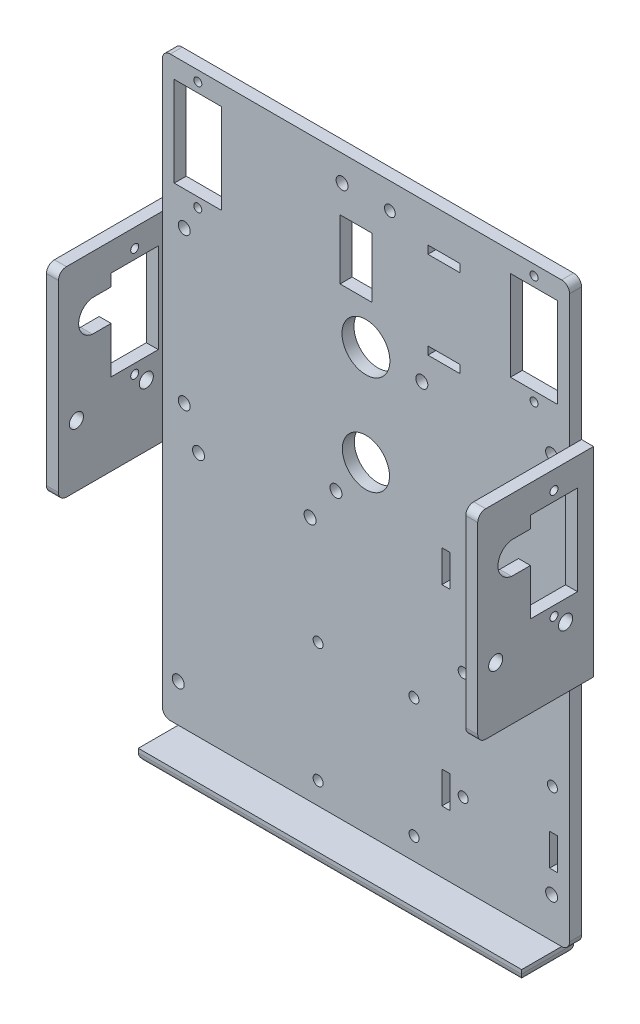
SolidWorks part; units mm, degrees
ref_plane "Alzado" through (0, 0, 0) normal (0, 0, 1) x (1, 0, 0)
ref_plane "Planta" through (0, 0, 0) normal (0, 1, 0) x (1, 0, 0)
ref_plane "Vista lateral" through (0, 0, 0) normal (1, 0, 0) x (0, 0, -1)
sketch "Model" plane through (0, 0, 0) normal (0, 0, 1) x (1, 0, 0)
  line L0 (13.199, -198.586) -> (108.1426, -198.586)
  line L1 (60.6708, -93.0989) -> (60.6708, -118.0989) construction
  line L2 (111.6708, -139.1347) -> (111.6708, -196.586)
  line L3 (111.6708, -139.1347) -> (114.6708, -139.1347)
  line L4 (114.6708, -89.1347) -> (114.6708, -139.1347)
  line L5 (111.6708, -89.1347) -> (114.6708, -89.1347)
  line L6 (111.6708, -56.021) -> (111.6708, -89.1347)
  line L7 (6.6708, -89.1347) -> (6.6708, -139.1347)
  line L8 (11.6708, -198.586) -> (13.199, -198.586)
  line L9 (109.6708, -198.586) -> (108.1426, -198.586)
  line L10 (77.899, -54.021) -> (43.5553, -54.021)
  line L13 (109.6708, -54.021) -> (77.899, -54.021)
  line L32 (9.6708, -139.1347) -> (9.6708, -196.586)
  line L35 (9.6708, -139.1347) -> (6.6708, -139.1347)
  line L37 (9.6708, -89.1347) -> (6.6708, -89.1347)
  line L40 (9.6708, -56.021) -> (9.6708, -89.1347)
  line L41 (43.5553, -54.021) -> (11.6708, -54.021)
  line L48 (54.199, -67.627) -> (54.199, -82.627)
  line L49 (54.199, -82.627) -> (62.199, -82.627)
  line L50 (62.199, -82.627) -> (62.199, -67.627)
  line L51 (62.199, -67.627) -> (54.199, -67.627)
  line L52 (76.199, -65.1868) -> (84.199, -65.1868)
  line L53 (84.199, -65.1868) -> (84.199, -63.1868)
  line L54 (84.199, -63.1868) -> (76.199, -63.1868)
  line L55 (76.199, -63.1868) -> (76.199, -65.1868)
  line L56 (76.199, -87.0675) -> (84.199, -87.0675)
  line L57 (84.199, -87.0675) -> (84.199, -85.0675)
  line L58 (84.199, -85.0675) -> (76.199, -85.0675)
  line L59 (76.199, -85.0675) -> (76.199, -87.0675)
  line L60 (96.8708, -59.021) -> (96.8708, -81.521)
  line L61 (96.8708, -81.521) -> (108.6708, -81.521)
  line L62 (108.6708, -81.521) -> (108.6708, -59.021)
  line L63 (108.6708, -59.021) -> (96.8708, -59.021)
  line L64 (24.4708, -59.021) -> (12.6708, -59.021)
  line L65 (12.6708, -59.021) -> (12.6708, -81.521)
  line L66 (12.6708, -81.521) -> (24.4708, -81.521)
  line L67 (24.4708, -81.521) -> (24.4708, -59.021)
  line L68 (81.699, -183.086) -> (81.699, -175.086)
  line L69 (81.699, -175.086) -> (79.699, -175.086)
  line L70 (79.699, -175.086) -> (79.699, -183.086)
  line L71 (79.699, -183.086) -> (81.699, -183.086)
  line L72 (108.6708, -183.086) -> (108.6708, -175.086)
  line L73 (108.6708, -175.086) -> (106.6708, -175.086)
  line L74 (106.6708, -175.086) -> (106.6708, -183.086)
  line L75 (106.6708, -183.086) -> (108.6708, -183.086)
  line L76 (81.699, -135.086) -> (81.699, -127.086)
  line L77 (81.699, -127.086) -> (79.699, -127.086)
  line L78 (79.699, -127.086) -> (79.699, -135.086)
  line L79 (79.699, -135.086) -> (81.699, -135.086)
  line L80 (109.199, -136.086) -> (109.199, -128.086)
  line L81 (109.199, -128.086) -> (107.199, -128.086)
  line L82 (107.199, -128.086) -> (107.199, -136.086)
  line L83 (107.199, -136.086) -> (109.199, -136.086)
  circle A10 centre (107.1708, -93.1139) radius 1.5
  circle A11 centre (102.7708, -56.621) radius 1
  circle A12 centre (102.7708, -83.921) radius 1
  circle A13 centre (18.5708, -83.921) radius 1
  circle A14 centre (18.5708, -56.621) radius 1
  circle A15 centre (60.6708, -93.0989) radius 6
  circle A16 centre (15.1708, -90.016) radius 1.5
  circle A17 centre (46.6908, -137.016) radius 1.5
  circle A18 centre (18.7508, -137.016) radius 1.5
  circle A19 centre (13.6708, -189.086) radius 1.5
  circle A20 centre (53.1708, -128.016) radius 1.5
  circle A21 centre (15.1708, -128.016) radius 1.5
  circle A22 centre (107.374, -165.0159) radius 1.25
  circle A23 centre (85.024, -151.5159) radius 1.25
  circle A24 centre (85.024, -178.5159) radius 1.25
  circle A25 centre (66.6708, -60.521) radius 1.3498
  circle A26 centre (107.1708, -188.586) radius 1.5
  circle A27 centre (74.6708, -93.5807) radius 1.5
  circle A28 centre (60.6708, -118.0989) radius 5.9
  circle A29 centre (54.699, -60.521) radius 1.5
  circle A30 centre (48.699, -193.086) radius 1.25
  circle A31 centre (72.7271, -193.086) radius 1.25
  circle A32 centre (72.699, -163.086) radius 1.25
  circle A33 centre (48.699, -163.086) radius 1.25
  arc A36 (111.6708, -56.021) -> (109.6708, -54.021) centre (109.6708, -56.021) ccw
  arc A41 (109.6708, -198.586) -> (111.6708, -196.586) centre (109.6708, -196.586) ccw
  arc A46 (9.6708, -196.586) -> (11.6708, -198.586) centre (11.6708, -196.586) ccw
  arc A50 (11.6708, -54.021) -> (9.6708, -56.021) centre (11.6708, -56.021) ccw
extrude "Saliente-Extruir1" add sketch "Model" along normal blind 3
sketch "Croquis2" plane through (0, 0, 0) normal (0, 0, -1) x (-1, 0, 0)
  line L0 (-114.6708, -89.1347) -> (-111.6708, -89.1347)
  line L1 (-111.6708, -89.1347) -> (-111.6708, -139.1347)
  line L2 (-111.6708, -139.1347) -> (-114.6708, -139.1347)
  line L3 (-114.6708, -139.1347) -> (-114.6708, -89.1347)
extrude "Saliente-Extruir2" add sketch "Croquis2" against normal blind 29
sketch "Croquis3" plane through (114.6708, 0, 0) normal (1, 0, 0) x (0, 0, -1)
  line L0 (-4, -118.6347) -> (-4, -96.1347)
  line L1 (-4, -96.1347) -> (-15.8, -96.1347)
  line L2 (-15.8, -118.6347) -> (-4, -118.6347)
  line L3 (-7, -123.7347) -> (-24.5, -123.7347) construction
  line L4 (-9.9, -93.7347) -> (-9.9, -121.0345) construction
  line L5 (-15.8, -107.0454) -> (-15.8, -118.6347)
  line L6 (-15.8, -96.1347) -> (-15.8, -99.1347)
  line L7 (-15.8, -99.1347) -> (-20.5775, -99.1347)
  line L8 (-20.4886, -107.0454) -> (-15.8, -107.0454)
  line L9 (-29, -89.1347) -> (0, -89.1347) construction
  line L10 (0, -139.1347) -> (0, -89.1347) construction
  circle A0 centre (-24.5, -123.7347) radius 1.7655
  circle A1 centre (-7, -123.7347) radius 1.7655
  circle A2 centre (-9.9, -121.0345) radius 1
  circle A3 centre (-9.9, -93.7347) radius 1
  arc A4 (-20.5775, -99.1347) -> (-20.4886, -107.0454) centre (-19.9386, -103.0834) ccw
  point P8 (-9.9, -96.1347)
  dimension "D1" = 2.4
  dimension "D2" = 2.3998
  dimension "D3" = 22.5
  dimension "D4" = 5.1
  dimension "D5" = 17.5
  dimension "D6" = 3
  dimension "D7" = 7
  dimension "D8" = 4
  dimension "D9" = 5.9
  dimension "D10" = 11.8
extrude "Cortar-Extruir1" cut sketch "Croquis3" against normal blind 3
fillet "Redondeo1" radius 2 2 edges at (113.1708, -139.1347, 29) (113.1708, -89.1347, 29)
ref_plane "Plano1" through (60.6708, 0, 0) normal (1, 0, 0) x (0, 0, -1)
mirror "Simetría1" about plane through (60.6708, 0, 0) normal (1, 0, 0) of "Redondeo1", "Cortar-Extruir1", "Saliente-Extruir2"
sketch "Croquis4" plane through (0, 0, 0) normal (0, 0, -1) x (-1, 0, 0)
  line L0 (-13.6708, -198.586) -> (-13.6708, -201.586)
  line L1 (-11.6708, -198.586) -> (-109.6708, -198.586) construction
  line L2 (-13.6708, -201.586) -> (-109.6708, -201.586)
  line L3 (-109.6708, -201.586) -> (-109.6708, -198.586)
  line L4 (-109.6708, -198.586) -> (-13.6708, -198.586)
  dimension "D1" = 3
  dimension "D2" = 96
extrude "Saliente-Extruir3" add sketch "Croquis4" against normal blind 13
fillet "Redondeo2" radius 2 4 edges at (13.6708, -201.586, 6.5) (109.6708, -201.586, 6.5) (61.6708, -201.586, 13) (61.6708, -201.586, 0)
